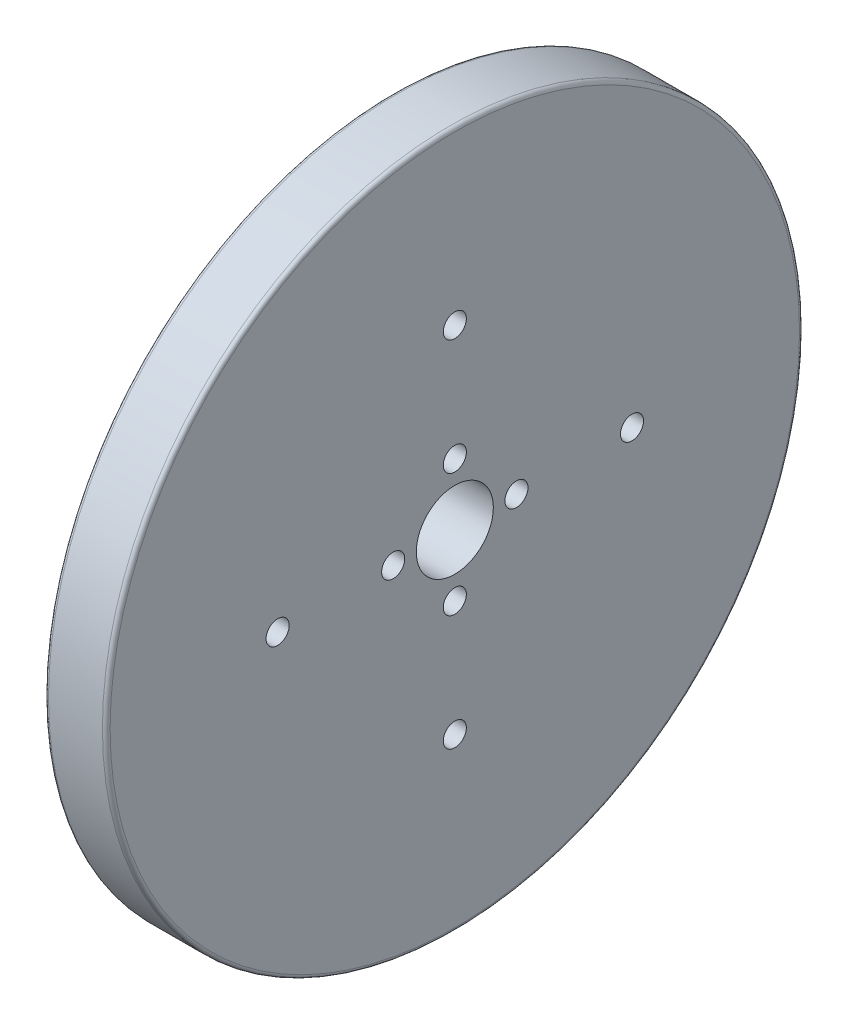
SolidWorks part; units mm, degrees
material "PMMA"
ref_plane "Front Plane" through (0, 0, 0) normal (0, 0, 1) x (1, 0, 0)
ref_plane "Top Plane" through (0, 0, 0) normal (0, 1, 0) x (1, 0, 0)
ref_plane "Right Plane" through (0, 0, 0) normal (1, 0, 0) x (0, 0, -1)
sketch "Sprocket" plane through (0, 0, 0) normal (1, 0, 0) x (0, 0, -1)
  circle A0 centre (0, 0) radius 45.25
  dimension "D1" = 90.5
extrude "Estrusione-Estrusione2" add sketch "Sprocket" along normal blind 8 contours A0
sketch "Schizzo1" plane through (0, 0, 0) normal (1, 0, 0) x (0, 0, -1)
  line L0 (0, 45.25) -> (0, -45.25) construction
  line L4 (-45.25, 0) -> (45.25, 0) construction
  circle A0 centre (0, 0) radius 5
  circle A1 centre (0, 23) radius 1.5
  circle A2 centre (8, 0) radius 1.5
  circle A3 centre (0, 8) radius 1.5
  circle A4 centre (23, 0) radius 1.5
  circle A5 centre (0, -8) radius 1.5
  circle A6 centre (0, -23) radius 1.5
  circle A7 centre (0, 0) radius 45.25 construction
  circle A8 centre (-8, 0) radius 1.5
  circle A9 centre (-23, 0) radius 1.5
  circle A10 centre (5.6569, 5.6569) radius 1.5 [skipped]
  circle A11 centre (-5.6569, 5.6569) radius 1.5 [skipped]
  circle A12 centre (-5.6569, -5.6569) radius 1.5 [skipped]
  circle A13 centre (5.6569, -5.6569) radius 1.5 [skipped]
  point P5 (0, 0)
  point P8 (0, 0)
  point P30 (0, 0)
  point P39 (0, 0)
  dimension "D1" = 10
  dimension "D2" = 3
  dimension "D5" = 3
  dimension "D3" = 8
  dimension "D6" = 15
  dimension "D4" = 8
  dimension "D7" = 4
extrude "Taglio-Estrusione2" cut sketch "Schizzo1" along direction (1, 0, 0) on the side of the normal through all
sketch "Schizzo2" plane through (0, 0, 0) normal (1, 0, 0) x (0, 0, -1)
  line L0 (0, 4) -> (0, 5) construction
  line L1 (3.9686, -0.5) -> (4.9749, -0.5)
  line L2 (-0.5, 4.9749) -> (-0.5, 3.9686)
  line L3 (0.5, 3.9686) -> (0.5, 4.9749)
  line L4 (4.9749, 0.5) -> (3.9686, 0.5)
  line L5 (-0.5, -3.9686) -> (-0.5, -4.9749)
  line L6 (0.5, -4.9749) -> (0.5, -3.9686)
  line L7 (-3.9686, 0.5) -> (-4.9749, 0.5)
  line L8 (-4.9749, -0.5) -> (-3.9686, -0.5)
  circle A0 centre (0, 0) radius 2
  circle A1 centre (0, 0) radius 4
  arc A3 (-0.5, 4.9749) -> (0.5, 4.9749) centre (0, 0) cw
  arc A4 (-0.5, 3.9686) -> (0.5, 3.9686) centre (0, 0) cw
  arc A5 (4.9749, 0.5) -> (4.9749, -0.5) centre (0, 0) cw
  arc A6 (3.9686, 0.5) -> (3.9686, -0.5) centre (0, 0) cw
  arc A7 (0.5, -4.9749) -> (-0.5, -4.9749) centre (0, 0) cw
  arc A8 (0.5, -3.9686) -> (-0.5, -3.9686) centre (0, 0) cw
  arc A9 (-4.9749, -0.5) -> (-4.9749, 0.5) centre (0, 0) cw
  arc A10 (-3.9686, -0.5) -> (-3.9686, 0.5) centre (0, 0) cw
  point P30 (0, 0)
  dimension "D1" = 4
  dimension "D2" = 8
  dimension "D3" = 0.5
  dimension "D5" = 4
  dimension "D4" = 0.5
extrude "Estrusione-Estrusione3" [suppressed] add sketch "Schizzo2" along normal blind 8 contours A1 A4 A0 | A9 L8 A1 L7 | A7 L6 A1 L5 | A5 L4 A1 L1
fillet "Raccordo1" radius 0.5 2 edges at (0, 0, -45.25) (8, 0, -45.25)
equation "\"Thickness8\"=8"
equation "\"D1@Estrusione-Estrusione2\"=\"Thickness8\""
equation "\"D\"= 90.5"
equation "\"D1@Sprocket\"=\"D\""
equation "\"D4@Schizzo1\"=\"D3@Schizzo1\""
equation "\"D1@Estrusione-Estrusione3\"=\"Thickness8\""
